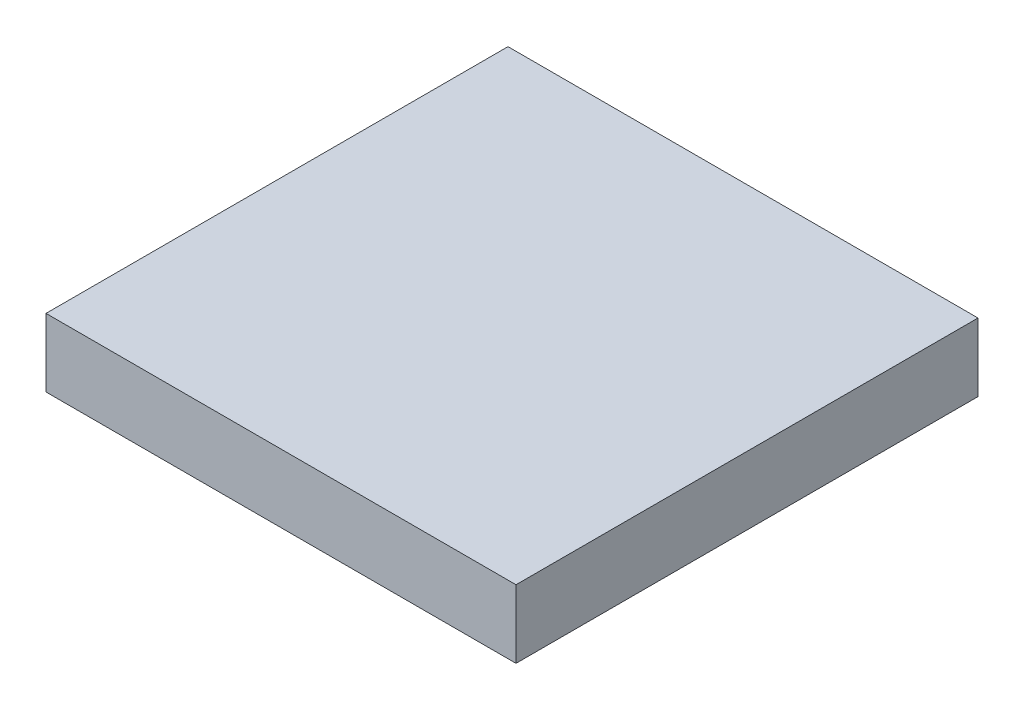
SolidWorks part; units mm, degrees
ref_plane "前基準面" through (0, 0, 0) normal (0, 0, 1) x (1, 0, 0)
ref_plane "上基準面" through (0, 0, 0) normal (0, 1, 0) x (1, 0, 0)
ref_plane "右基準面" through (0, 0, 0) normal (1, 0, 0) x (0, 0, -1)
sketch "草圖1" plane through (0, 0, 0) normal (0, 1, 0) x (1, 0, 0)
  line L1 (-73.7846, 33.8462) -> (102.2154, 33.8462)
  line L2 (-73.7846, 33.8462) -> (-73.7846, -139.1538)
  line L3 (-73.7846, -139.1538) -> (102.2154, -139.1538)
  line L4 (102.2154, 33.8462) -> (102.2154, -139.1538)
  dimension "D1" = 176
  dimension "D2" = 173
extrude "填料-伸長1" add sketch "草圖1" along normal blind 25.5
sketch "草圖4" plane through (102.2154, 0, 0) normal (1, 0, 0) x (0, 0, -1)
  line L0 (-139.1538, 0) -> (33.8462, 0) construction
  line L1 (-139.1538, 25.5) -> (33.8462, 25.5) construction
  line L2 (-59.6538, 176) -> (-57.6538, 176)
  line L3 (-47.6538, 176) -> (-45.6538, 176)
  line L4 (-44.6538, 55.5) -> (-42.6538, 55.5)
  line L5 (-32.6538, 55.5) -> (-30.6538, 55.5)
  arc A0 (-57.6538, 176) -> (-47.6538, 176) centre (-52.6538, 176) ccw
  arc A1 (-59.6538, 176) -> (-45.6538, 176) centre (-52.6538, 176) ccw
  arc A2 (-42.6538, 55.5) -> (-32.6538, 55.5) centre (-37.6538, 55.5) ccw
  arc A3 (-44.6538, 55.5) -> (-30.6538, 55.5) centre (-37.6538, 55.5) ccw
  point P0 (-52.6538, 176)
  point P3 (-37.6538, 55.5)
  point P10 (0, 0)
  point P11 (0, 0)
  point P18 (0, 0)
  point P19 (0, 0)
  point P20 (0, 0)
  point P21 (0, 0)
  dimension "D4" = 10
  dimension "D5" = 14
  dimension "D6" = 10
  dimension "D7" = 14
  dimension "D1" = 176
  dimension "D2" = 15
  dimension "D3" = 30
sketch "草圖5" plane through (0, 25.5, 0) normal (0, 1, 0) x (1, 0, 0)
  circle A0 centre (0, 0) radius 5
  dimension "D1" = 10
sketch "草圖7" plane through (0, 25.5, 0) normal (0, 1, 0) x (1, 0, 0)
  circle A0 centre (0, -52.6538) radius 60
  dimension "D1" = 120
curve "螺旋曲線/渦捲線2" pitch 13 height 130 turns 10
ref_plane "平面1" through (0, 0, 52.6538) normal (0, 0, 1) x (1, 0, 0)
sketch "草圖8" plane through (0, 0, 52.6538) normal (0, 0, 1) x (1, 0, 0)
  line L0 (102.2154, 176) -> (-90.3077, 151.6591)
  point P0 (102.2154, 176)
